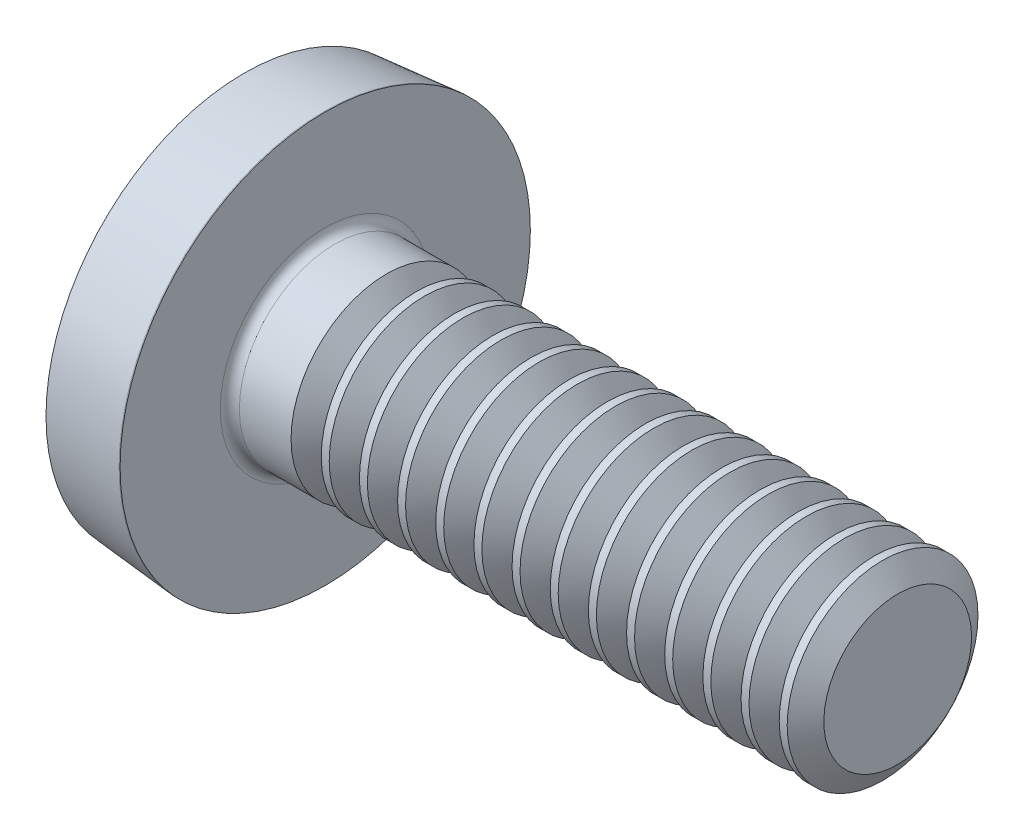
SolidWorks part; units mm, degrees
ref_plane "Plane1" through (0, 0, 0) normal (0, 0, 1) x (1, 0, 0)
ref_plane "Plane2" through (0, 0, 0) normal (0, 1, 0) x (1, 0, 0)
ref_plane "Plane3" through (0, 0, 0) normal (1, 0, 0) x (0, 0, -1)
sketch "BodySke" plane through (0, 0, 0) normal (0, 0, 1) x (1, 0, 0)
  line L0 (1.2, 1) -> (1.2, 2.15)
  line L1 (1.6, 6.35) -> (1.6, -3.175) construction
  line L2 (-25.4, 0) -> (127, 0) construction
  line L3 (7.2, 0) -> (0, 0)
  line L4 (1.2, 1) -> (7.2, 1)
  line L5 (7.2, 1) -> (7.2, 0)
  line L6 (0.35, 2.0765) -> (1.19, 2.15)
  line L8 (1.2, 6.35) -> (1.2, -3.175) construction
  line L9 (1.2, 2.15) -> (1.19, 2.15)
  arc A0 (0.35, 2.0765) -> (0, 0) centre (6.3348, 0) ccw
  dimension "Length" = 6
  dimension "Head_ht" = 1.2
  dimension "Advance" = 0.4
  dimension "Thread_nom" = 6
  dimension "Diameter" = 2
  dimension "Head_dia" = 4.3
  dimension "Head_ang" = 85
  dimension "Oval_ht" = 0.35
  dimension "D1" = 0.01
revolve "Base-Revolve" add sketch "BodySke"
cosmetic thread "ThreadCosmetic" [suppressed]
fillet "Fillet1" radius 0.1 1 edges at (1.2, 0, 1)
sketch "Sketch3" plane through (0, 0, 0) normal (1, 0, 0) x (0, 0, -1)
  line L0 (0.37, -1.1) -> (-0.37, -1.1)
  line L1 (0.37, -1.1) -> (0.37, 1.1)
  line L2 (-0.37, 1.1) -> (0.37, 1.1)
  line L3 (-0.37, 1.1) -> (-0.37, -1.1)
  dimension "Cross_dia" = 2.2
  dimension "D1" = 1.1
  dimension "Cross_width" = 0.74
  dimension "D2" = 0.37
ref_plane "Plane4" through (1.01, 0, 0) normal (1, 0, 0) x (0, 0, -1)
sketch "Sketch4" plane through (1.01, 0, 0) normal (1, 0, 0) x (0, 0, -1)
  line L0 (0.37, -0.5964) -> (-0.37, -0.5964)
  line L1 (0.37, -0.5964) -> (0.37, 0.5964)
  line L2 (-0.37, 0.5964) -> (0.37, 0.5964)
  line L3 (-0.37, 0.5964) -> (-0.37, -0.5964)
  dimension "D1" = 0.74
  dimension "D2" = 1.1929
  dimension "D3" = 0.37
  dimension "D4" = 0.5964
loft "Recess" cut profiles "Sketch3", "Sketch4"
pattern_circular "RecPat" count 2 every 90 about axis through (0, 0, 0) along (1, 0, 0) of "Recess"
sketch "RecCorSke" plane through (0, 0, 0) normal (0, 0, 1) x (1, 0, 0)
  line L0 (-3.175, 0) -> (15.875, 0) construction
  line L1 (-25.4, 0) -> (127, 0) construction
  line L2 (0, 0) -> (0, 0.6266)
  line L3 (0, 0.6266) -> (1.01, 0.556)
  line L4 (1.01, 0.556) -> (1.1907, 0)
  line L5 (1.1907, 0) -> (0, 0)
  dimension "Diameter" = 1.112
  dimension "Depth" = 1.01
  dimension "Draft_angle" = 4
  dimension "Bottom_angle" = 18
revolve "RecessCore" cut sketch "RecCorSke" angle 360 about L0
sketch "ThdSchSke" plane through (0, 0, 0) normal (0, 0, 1) x (1, 0, 0)
  line L0 (2, -0.774) -> (1.8418, -1)
  line L1 (2, -0.774) -> (2.1582, -1)
  line L2 (2.1582, -1) -> (2.1582, -1.25)
  line L3 (-3.175, 0) -> (5.1513, 0) construction
  line L5 (2.1582, -1.25) -> (1.8418, -1.25)
  line L6 (1.8418, -1.25) -> (1.8418, -1)
  dimension "Diameter" = 2
  dimension "SideAngle" = 55
  dimension "VeeAngle" = 70
  dimension "Thread_minor" = 1.548
  dimension "Overcut" = 2.5
  dimension "Start" = 2
revolve "ThreadSchematic" cut sketch "ThdSchSke" angle 360 about L3
pattern_linear "ThdSchPat" count 14 spacing 0.4 along (1, 0, 0) of "ThreadSchematic"
equation "' \"Diameter@BodySke\" = 8"
equation "' \"Length@BodySke\" = 35"
equation "' \"Head_dia@BodySke\" = 16.4"
equation "' \"Oval_ht@BodySke\" = 1.7"
equation "' \"Head_ht@BodySke\" = 4.8"
equation "' \"Thread_nom@BodySke\" =  30"
equation "' \"Thread_nom@BodySke\" = 30"
equation "' \"Head_ang@BodySke\" = 85"
equation "' \"Cross_dia@Sketch3\" = 7.8"
equation "' \"Cross_width@Sketch3\" = 1.42"
equation "' \"Cross_depth@Plane4\" = 4.36"
equation "' \"Diameter@RecCorSke\" = 2.561"
equation "' \"Radius@Fillet1\" = 0.4"
equation "' \"Thread_minor@ThreadCosmetic\" = 6.619"
equation "' \"Advance@BodySke\" = 1.25"
equation "\"D1@Sketch3\" = \"Cross_dia@Sketch3\" / 2"
equation "\"D2@Sketch3\" = \"Cross_width@Sketch3\" / 2"
equation "\"Depth@RecCorSke\" = \"Cross_depth@Plane4\""
equation "\"D1@Sketch4\" = \"Cross_width@Sketch3\""
equation "\"D2@Sketch4\" = \"Cross_dia@Sketch3\" - 2.0 * \"Cross_depth@Plane4\" * tan(26.5  * 0.017453292)"
equation "\"D3@Sketch4\" = \"D1@Sketch4\" / 2"
equation "\"D4@Sketch4\" = \"D2@Sketch4\" / 2"
equation "\"Thread_length@ThreadCosmetic\" = ((sgn( (\"Length@BodySke\" - \"Advance@BodySke\" * 2.0 ) - \"Thread_nom@BodySke\" )-1)*( (\"Length@BodySke\" - \"Advance@BodySke\" * 2.0 ) - \"Thread_nom@BodySke\" ))/-2+ \"Thread_nom@BodySke\""
equation "\"Thread_minor@ThdSchSke\" = \"Thread_minor@ThreadCosmetic\""
equation "\"Diameter@ThdSchSke\" = \"Diameter@BodySke\""
equation "\"Overcut@ThdSchSke\" = \"Diameter@BodySke\" * 1.25"
equation "\"Start@ThdSchSke\" = \"Head_ht@BodySke\" + \"Length@BodySke\" - \"Thread_length@ThreadCosmetic\"  '---Non-countersunk---"
equation "\"Num_threads@ThdSchPat\" = int( \"Thread_length@ThreadCosmetic\" / \"Advance@BodySke\" + 0.999 )  + 1"
equation "\"Advance@ThdSchPat\" = \"Thread_length@ThreadCosmetic\" /  (\"Num_threads@ThdSchPat\" - 1) 'relax it"
